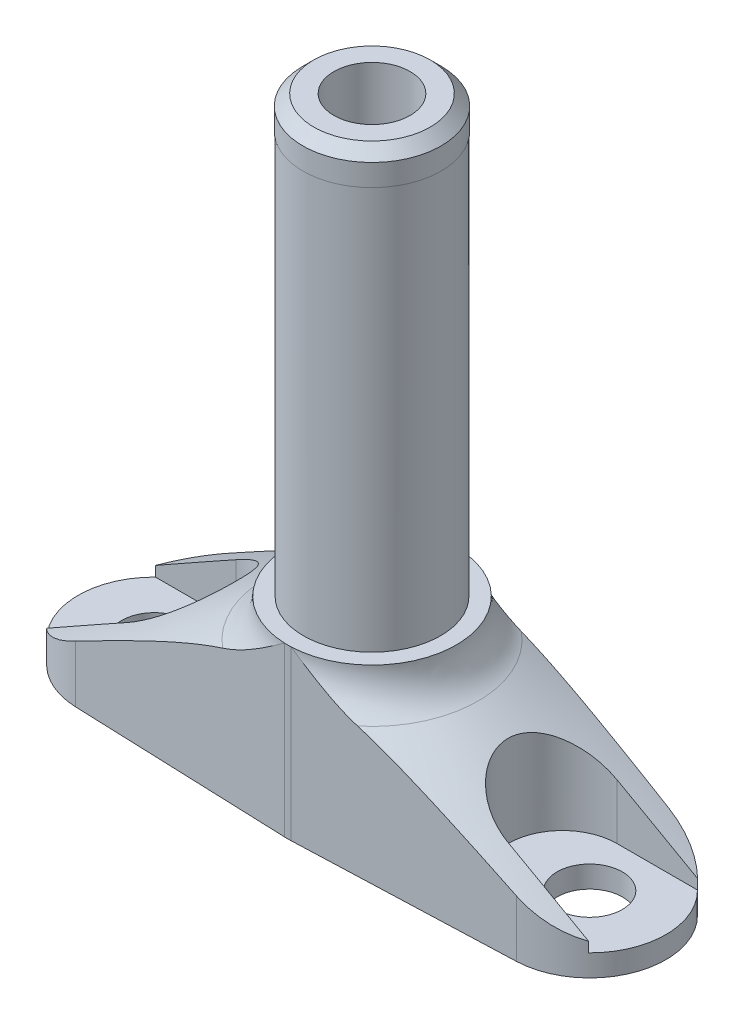
SolidWorks part; units mm, degrees
material "7075-T6 (SN)"
ref_plane "Płaszczyzna XY" through (0, 0, 0) normal (0, 0, 1) x (1, 0, 0)
ref_plane "Płaszczyzna XZ" through (0, 0, 0) normal (0, 1, 0) x (1, 0, 0)
ref_plane "Płaszczyzna YZ" through (0, 0, 0) normal (1, 0, 0) x (0, 0, -1)
sketch "Szkic1" plane through (0, 0, 0) normal (0, 0, 1) x (1, 0, 0)
  line L0 (0, 0) -> (0, 25) construction
  line L1 (0, 0) -> (0, 25)
  line L2 (0, 0) -> (27, 0)
  line L4 (0, 25) -> (27, 25)
  line L5 (27, 0) -> (27, 25)
  dimension "D1" = 54
  dimension "D2" = 25
revolve "Obrót1" add sketch "Szkic1" angle 360 about L0
sketch "Szkic2" plane through (0, 0, 0) normal (0, 0, 1) x (1, 0, 0)
  line L0 (0, 0) -> (0, 25) construction
  line L1 (27, 25) -> (-27, 25) construction
  line L2 (0, 25) -> (7.75, 25) construction
  line L3 (7.75, 25) -> (7.75, 13.114)
  line L4 (7.75, 13.114) -> (27, 2)
  line L5 (27, 0) -> (27, 25) construction
  line L6 (-27, 0) -> (27, 0) construction
  line L7 (7.75, 25) -> (27, 25)
  line L8 (27, 25) -> (27, 2)
  dimension "D1" = 2
  dimension "D2" = 30
  dimension "D3" = 15.5
revolve "Wycięcie-obrót1" cut sketch "Szkic2" angle 360 about L0
fillet "Zaokrąglenie1" radius 4 1 edges at (0, 13.114, -7.75)
ref_plane "Płaszczyzna1" through (0, 2, 0) normal (0, 1, 0) x (1, 0, 0)
sketch "Szkic4" plane through (0, 2, 0) normal (0, 1, 0) x (1, 0, 0)
  line L0 (0, 8.8242) -> (0, -11.1289) construction
  circle A0 centre (-20, 0) radius 3
  circle A1 centre (20, 0) radius 3
  dimension "D1" = 6
  dimension "D2" = 6
  dimension "D3" = 40
extrude "Wytnij-wyciągnięcie3" cut sketch "Szkic4" against normal through all and the other way through all
sketch "Szkic3" plane through (0, 2, 0) normal (0, 1, 0) x (1, 0, 0)
  line L0 (-17.5, 5) -> (-26.533, 5)
  line L13 (-17.5, -5) -> (-26.533, -5)
  line L14 (17.5, 5) -> (26.533, 5)
  line L15 (17.5, -5) -> (26.533, -5)
  line L16 (0, 21.1527) -> (0, -20.0817) construction
  arc A1 (-17.5, -5) -> (-17.5, 5) centre (-17.5, 0) ccw
  arc A2 (17.5, 5) -> (17.5, -5) centre (17.5, 0) ccw
  circle A3 centre (0, 0) radius 27 construction
  arc A4 (-26.533, 5) -> (-26.533, -5) centre (0, 0) ccw
  arc A5 (26.533, -5) -> (26.533, 5) centre (0, 0) ccw
  dimension "D1" = 10
  dimension "D2" = 10
  dimension "D3" = 35
extrude "Wytnij-wyciągnięcie2" cut sketch "Szkic3" along normal through all
sketch "Szkic5" plane through (0, 0, 0) normal (0, -1, 0) x (1, 0, 0)
  line L0 (-20.2625, 6.9951) -> (-0.2906, 7.7445)
  line L1 (-20.2625, -6.9951) -> (-0.2906, -7.7445)
  line L2 (0.2906, 7.7445) -> (20.2625, 6.9951)
  line L3 (20.2625, -6.9951) -> (0.2906, -7.7445)
  arc A0 (-0.2906, -7.7445) -> (0.2906, -7.7445) centre (0, 0) ccw
  arc A1 (-20.2625, 6.9951) -> (-20.2625, -6.9951) centre (-20, 0) ccw
  arc A2 (20.2625, -6.9951) -> (20.2625, 6.9951) centre (20, 0) ccw
  circle A3 centre (0, 0) radius 27 construction
  arc A4 (0.2906, 7.7445) -> (-0.2906, 7.7445) centre (0, 0) ccw
  dimension "D1" = 15.5
extrude "Wytnij-wyciągnięcie4" cut sketch "Szkic5" against normal through all flip side to cut
sketch "Szkic8" plane through (0, 0, 0) normal (0, 0, 1) x (1, 0, 0)
  line L0 (7.75, 25) -> (-7.75, 25) construction
  line L1 (0, 25) -> (7.75, 25)
  line L2 (0, 25) -> (0, 15.4234)
  line L3 (0, 15.4234) -> (7.75, 15.4234)
  line L4 (7.75, 25) -> (7.75, 15.4234)
revolve "Wycięcie-obrót2" cut sketch "Szkic8" angle 360 about L2
sketch "Szkic9" plane through (0, 0, 0) normal (0, 0, 1) x (1, 0, 0)
  line L0 (7.75, 15.4234) -> (0.2906, 15.4234) construction
  line L1 (0, 15.4234) -> (6.3, 15.4234)
  line L2 (0, 15.4234) -> (0, 55.4234) construction
  line L3 (0, 55.4234) -> (5.35, 55.4234)
  line L4 (6.3, 15.4234) -> (6.3, 52.4234)
  line L5 (5.35, 55.4234) -> (6.35, 54.4234)
  line L6 (0, 55.4234) -> (6.35, 55.4234)
  line L7 (0, 55.4234) -> (0, 52.4234) construction
  line L8 (6.3, 52.4234) -> (6.35, 52.4234)
  line L9 (6.35, 54.4234) -> (6.35, 52.4234)
  line L10 (0, 15.4234) -> (0, 55.4234)
  dimension "D1" = 40
  dimension "D2" = 12.6
  dimension "D3" = 12.7
  dimension "D4" = 3
revolve "Obrót2" add sketch "Szkic9" angle 360 about L2
sketch "Szkic10" plane through (0, 55.4234, 0) normal (0, 1, 0) x (1, 0, 0)
  circle A0 centre (0, 0) radius 3.5
  dimension "D1" = 7
extrude "Wytnij-wyciągnięcie5" cut sketch "Szkic10" against normal through all
equation "\"D3@Szkic3\"=40-2*1/2*5"
